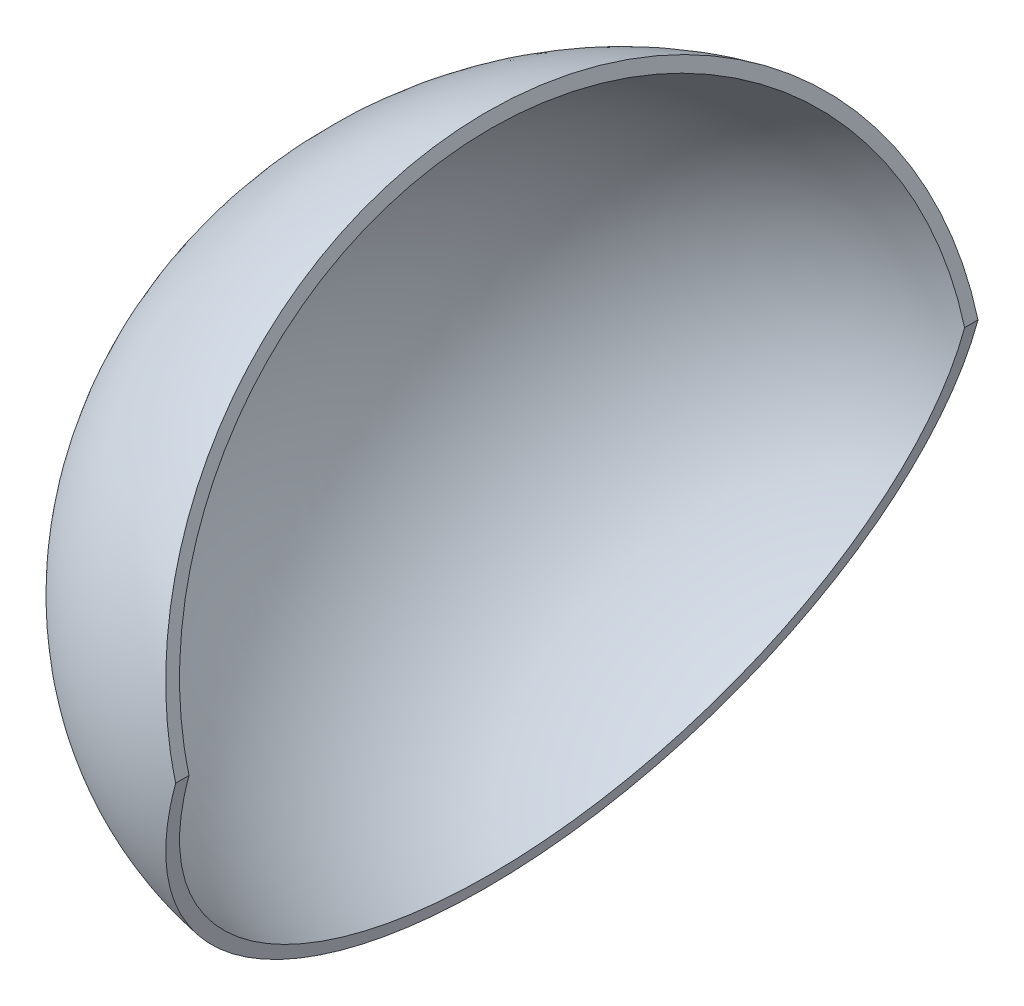
SolidWorks part; units mm, degrees
other "Markup1"
sketch "Sketch6"
ref_plane "Front Plane" through (0, 0, 0) normal (0, 0, 1) x (1, 0, 0)
ref_plane "Top Plane" through (0, 0, 0) normal (0, 1, 0) x (1, 0, 0)
ref_plane "Right Plane" through (0, 0, 0) normal (1, 0, 0) x (0, 0, -1)
sketch "Sketch4" plane through (0, 0, 0) normal (0, 1, 0) x (1, 0, 0)
  line L0 (0, 15) -> (0, 14.5)
  line L1 (0, -14.5) -> (0, -15)
  line L2 (0, 15) -> (0, -15) construction
  line L3 (0, 0) -> (-13, 0) construction
  line L4 (-13, 0) -> (-17, 0) construction
  arc A0 (-13.6095, 6.4923) -> (-10.5837, 8.7103) centre (-14.8367, 11.3393) ccw
  arc A1 (-10.5837, -8.7103) -> (-13.6095, -6.4923) centre (-14.8367, -11.3393) ccw
  ellipse E0 centre (0, 0) end of major axis (0, -15) minor radius 13 (0, 15) -> (-10.5837, 8.7103) ccw
  ellipse E1 centre (-13, 0) end of major axis (-13, -6.569) minor radius 4 (-13.6095, 6.4923) -> (-13.6095, -6.4923) ccw
  ellipse E2 centre (0, 0) end of major axis (0, 15) minor radius 13 (-10.5837, 8.7103) -> (0, -15) ccw
  ellipse E3 centre (0, 0) end of major axis (0, -15) minor radius 13 (-10.5837, -8.7103) -> (0, -15) ccw
  ellipse E4 centre (0, 0) end of major axis (0, -15) minor radius 13 (-13, 0) -> (-10.5837, -8.7103) ccw
  spline S1 degree 3 poles (0, 14.5) (-1.6277, 14.5) (-4.8778, 13.7549) (-9.0419, 10.5501) (-11.842, 5.7194) (-12.829, 0) (-11.842, -5.7194) (-9.0419, -10.5501) (-4.8778, -13.7549) (-1.6277, -14.5) (0, -14.5) knots 0 0 0 0 0.392699 0.785398 1.178097 1.570796 1.963495 2.356194 2.748894 3.141593 3.141593 3.141593 3.141593
  dimension "D1" = 5
  dimension "D3" = 5
  dimension "D2" = 4
  dimension "D4" = 32.938
revolve "Revolve2" add sketch "Sketch4" angle 75 about L2
ref_plane "Plane1" through (-9, 0, 0) normal (1, 0, 0) x (0, 0, -1)
sketch "Sketch5" plane through (-9, 0, 0) normal (1, 0, 0) x (0, 0, -1)
  line L0 (-5.5, 5.5) -> (5.5, 5.5)
  line L1 (-5, -5) -> (5, -5)
  line L2 (-5, -5) -> (-5, 5)
  line L3 (-5, 5) -> (5, 5)
  line L4 (5, -5) -> (5, 5)
  line L5 (-5, -5) -> (5, 5) construction
  line L6 (-5, 5) -> (5, -5) construction
  line L7 (5.5, -5.5) -> (5.5, 5.5)
  line L8 (-5.5, -5.5) -> (5.5, -5.5)
  line L9 (-5.5, -5.5) -> (-5.5, 5.5)
  point P0 (0, 0)
  dimension "D2" = 10
  dimension "D3" = 10
  dimension "D1" = 0.5
